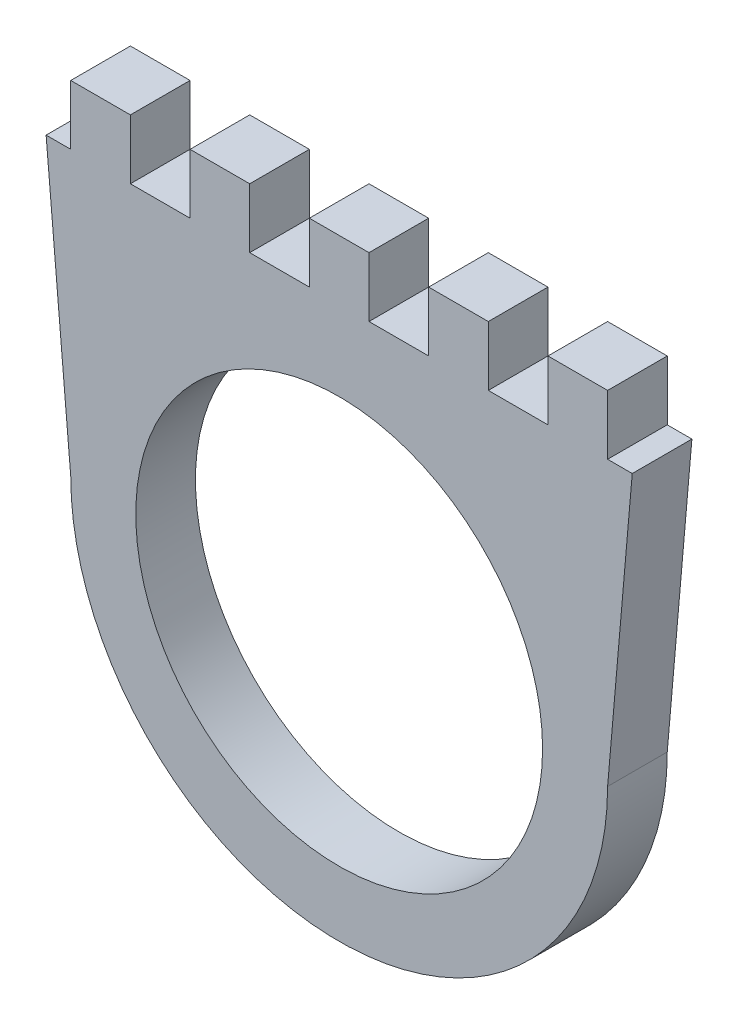
SolidWorks part; units mm, degrees
ref_plane "Plan de face" through (0, 0, 0) normal (0, 0, 1) x (1, 0, 0)
ref_plane "Plan de dessus" through (0, 0, 0) normal (0, 1, 0) x (1, 0, 0)
ref_plane "Plan de droite" through (0, 0, 0) normal (1, 0, 0) x (0, 0, -1)
sketch "Esquisse3" plane through (0, 0, 0) normal (0, 0, 1) x (1, 0, 0)
  line L0 (0, 70.5597) -> (0, -65.6935) construction
  line L1 (-22.5, 0) -> (-25, 28.75)
  line L2 (-25, 28.75) -> (25, 28.75)
  line L3 (25, 28.75) -> (22.5, 0)
  circle A0 centre (0, 0) radius 22.5 construction
  arc A1 (22.5, 0) -> (-22.5, 0) centre (0, 0) cw
  dimension "D1" = 45
  dimension "D2" = 25
  dimension "D3" = 50
  dimension "D4" = 28.75
extrude "Boss.-Extru.12" add sketch "Esquisse3" along normal blind 5
sketch "Esquisse4" plane through (0, 0, 5) normal (0, 0, 1) x (1, 0, 0)
  circle A0 centre (0, 0) radius 17.05
  dimension "D1" = 34.1
extrude "Enlèv. mat.-Extru.1" cut sketch "Esquisse4" against normal blind 5
sketch "Esquisse5" plane through (0, 0, 5) normal (0, 0, 1) x (1, 0, 0)
  line L0 (25, 28.75) -> (-25, 28.75) construction
  line L1 (-17.5, 28.75) -> (-12.5, 28.75)
  line L2 (-17.5, 28.75) -> (-17.5, 23.75)
  line L3 (-17.5, 23.75) -> (-12.5, 23.75)
  line L4 (-12.5, 28.75) -> (-12.5, 23.75)
  dimension "D1" = 5
  dimension "D2" = 5
  dimension "D3" = 7.5
extrude "Enlèv. mat.-Extru.2" cut sketch "Esquisse5" against normal blind 10
pattern_linear "Répétition linéaire1" count 4 spacing 10 along (1, 0, 0) of "Enlèv. mat.-Extru.2"
sketch "Esquisse6" plane through (0, 0, 5) normal (0, 0, 1) x (1, 0, 0)
  line L1 (22.5, 38.0077) -> (35.8299, 38.0077)
  line L2 (22.5, 38.0077) -> (22.5, 23.75)
  line L3 (22.5, 23.75) -> (35.8299, 23.75)
  line L4 (35.8299, 38.0077) -> (35.8299, 23.75)
  line L5 (-32.5806, 57.0618) -> (-22.5, 57.0618)
  line L6 (-32.5806, 57.0618) -> (-32.5806, 23.75)
  line L7 (-32.5806, 23.75) -> (-22.5, 23.75)
  line L8 (-22.5, 57.0618) -> (-22.5, 23.75)
  line L9 (-17.5, 28.75) -> (-17.5, 23.75) construction
  line L10 (17.5, 23.75) -> (17.5, 28.75) construction
  line L11 (25, 28.75) -> (17.5, 28.75) construction
  line L13 (-17.5, 28.75) -> (-25, 28.75) construction
  dimension "D1" = 5
  dimension "D2" = 5
  dimension "D3" = 5
  dimension "D4" = 5
extrude "Enlèv. mat.-Extru.3" cut sketch "Esquisse6" against normal blind 10
